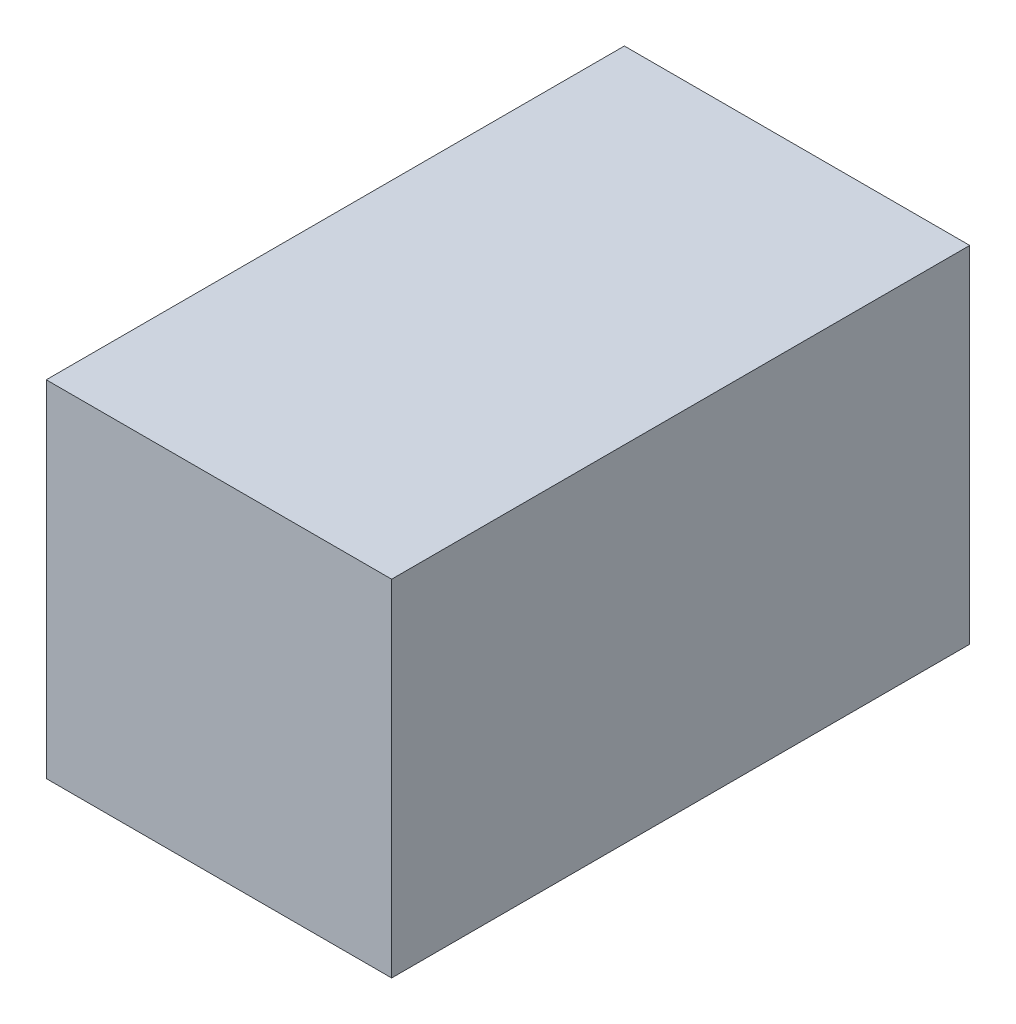
SolidWorks part; units mm, degrees
ref_plane "Front Plane" through (0, 0, 0) normal (0, 0, 1) x (1, 0, 0)
ref_plane "Top Plane" through (0, 0, 0) normal (0, 1, 0) x (1, 0, 0)
ref_plane "Right Plane" through (0, 0, 0) normal (1, 0, 0) x (0, 0, -1)
sketch "Sketch1" plane through (0, 0, 0) normal (0, 0, 1) x (1, 0, 0)
  line L1 (-22.225, 22.225) -> (22.225, 22.225)
  line L2 (-22.225, 22.225) -> (-22.225, -22.225)
  line L3 (-22.225, -22.225) -> (22.225, -22.225)
  line L4 (22.225, 22.225) -> (22.225, -22.225)
  line L5 (-22.225, 22.225) -> (22.225, -22.225) construction
  line L6 (-22.225, -22.225) -> (22.225, 22.225) construction
  point P0 (0, 0)
  dimension "D1" = 44.45
  dimension "D2" = 44.45
extrude "Boss-Extrude1" add sketch "Sketch1" along normal blind 35 and the other way blind 39.4
